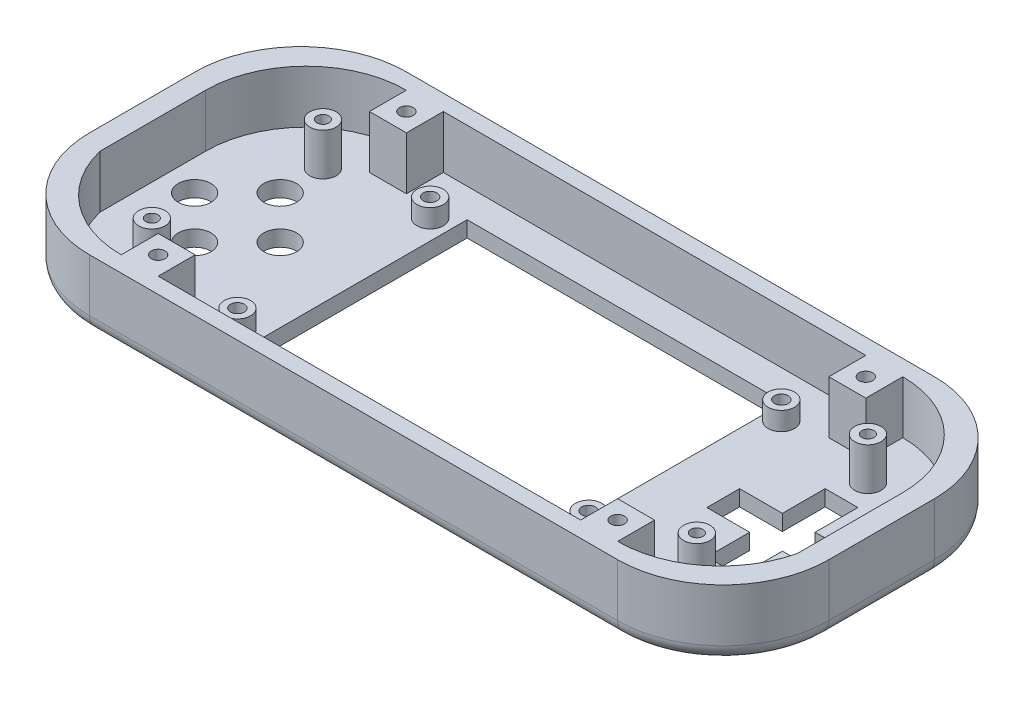
SolidWorks part; units mm, degrees
ref_plane "Front Plane" through (0, 0, 0) normal (0, 0, 1) x (1, 0, 0)
ref_plane "Top Plane" through (0, 0, 0) normal (0, 1, 0) x (1, 0, 0)
ref_plane "Right Plane" through (0, 0, 0) normal (1, 0, 0) x (0, 0, -1)
sketch "Sketch1" plane through (0, 0, 0) normal (0, 1, 0) x (1, 0, 0)
  line L0 (70, 10) -> (70, -10)
  line L1 (-50, 30) -> (50, 30)
  line L2 (-70, 10) -> (-70, -10)
  line L3 (-50, -30) -> (50, -30)
  line L5 (-50, 30) -> (50, -30) construction
  line L6 (-50, -30) -> (50, 30) construction
  arc A0 (-50, 30) -> (-70, 10) centre (-50, 10) ccw
  arc A1 (50, 30) -> (70, 10) centre (50, 10) cw
  arc A2 (-50, -30) -> (-70, -10) centre (-50, -10) cw
  arc A3 (50, -30) -> (70, -10) centre (50, -10) ccw
  point P0 (0, 0)
  dimension "D1" = 100
extrude "Boss-Extrude1" add sketch "Sketch1" along normal blind 3
sketch "Sketch2" plane through (0, 3, 0) normal (0, 1, 0) x (1, 0, 0)
  line L0 (-50, -30) -> (50, -30) construction
  line L1 (-47, 27) -> (47, 27)
  line L2 (-50, 30) -> (50, 30)
  line L3 (-47, -27) -> (47, -27)
  line L4 (70, 10) -> (70, -10)
  line L5 (-47, 27) -> (47, -27) construction
  line L6 (-47, -27) -> (47, 27) construction
  line L7 (-50, -30) -> (50, -30)
  line L8 (66, 8) -> (66, -12)
  line L9 (-50, 30) -> (50, -30) construction
  line L10 (-50, -30) -> (50, 30) construction
  line L11 (-70, 10) -> (-70, -10)
  line L13 (-66, 8) -> (-66, -12)
  arc A0 (-50, 30) -> (-70, 10) centre (-50, 10) ccw
  arc A1 (50, 30) -> (70, 10) centre (50, 10) cw
  arc A2 (-50, -30) -> (-70, -10) centre (-50, -10) cw
  arc A3 (50, -30) -> (70, -10) centre (50, -10) ccw
  arc A4 (47, 27) -> (66, 8) centre (47, 8) cw
  arc A5 (47, -27) -> (66, -12) centre (47, -7.4667) ccw
  arc A6 (-47, 27) -> (-66, 8) centre (-47, 8) ccw
  arc A7 (-47, -27) -> (-66, -12) centre (-47, -7.4667) cw
  point P0 (0, 0)
  point P8 (0, 0)
  dimension "D3" = 100
  dimension "D4" = 60
  dimension "D5" = 20
  dimension "D1" = 54
  dimension "D2" = 94
  dimension "D6" = 54
  dimension "D7" = 20
  dimension "D8" = 4
  dimension "D9" = 4
  dimension "D10" = 3
  dimension "D11" = 3
extrude "Boss-Extrude2" add sketch "Sketch2" along normal blind 10
sketch "Sketch3" plane through (0, 3, 0) normal (0, 1, 0) x (1, 0, 0)
  line L1 (-30, 21.5) -> (30, 21.5)
  line L2 (-30, 21.5) -> (-30, -21.5)
  line L3 (-30, -21.5) -> (30, -21.5)
  line L4 (30, 21.5) -> (30, -21.5)
  line L5 (-30, 21.5) -> (30, -21.5) construction
  line L6 (-30, -21.5) -> (30, 21.5) construction
  point P0 (0, 0)
  dimension "D1" = 43
  dimension "D2" = 60
extrude "Cut-Extrude1" cut sketch "Sketch3" against normal blind 5
sketch "Sketch4" plane through (0, 3, 0) normal (0, 1, 0) x (1, 0, 0)
  line L0 (30, 21.5) -> (-30, 21.5) construction
  line L1 (-30, 21.5) -> (-30, -21.5) construction
  line L2 (-30, -21.5) -> (30, -21.5) construction
  line L3 (30, -21.5) -> (30, 21.5) construction
  circle A0 centre (-33.75, 18.25) radius 2.5
  circle A1 centre (-33.75, -18.25) radius 2.5
  circle A2 centre (32.75, -18.25) radius 2.5
  circle A3 centre (32.75, 18.25) radius 2.5
  dimension "D1" = 5
  dimension "D4" = 5
  dimension "D5" = 3.25
  dimension "D7" = 5
  dimension "D10" = 5
  dimension "D2" = 3.25
  dimension "D3" = 3.75
  dimension "D6" = 3.75
  dimension "D8" = 3.25
  dimension "D9" = 2.75
  dimension "D11" = 2.75
  dimension "D12" = 3.25
extrude "Boss-Extrude3" add sketch "Sketch4" along normal blind 3.5
sketch "Sketch5" plane through (0, 6.5, 0) normal (0, 1, 0) x (1, 0, 0)
  circle A0 centre (-33.75, -18.25) radius 1.3
  dimension "D1" = 2.6
extrude "Cut-Extrude2" cut sketch "Sketch5" against normal blind 4.5
sketch "Sketch6" plane through (0, 6.5, 0) normal (0, 1, 0) x (1, 0, 0)
  circle A0 centre (-33.75, 18.25) radius 1.3
  dimension "D1" = 2.6
extrude "Cut-Extrude3" cut sketch "Sketch6" against normal blind 4.5
sketch "Sketch7" plane through (0, 6.5, 0) normal (0, 1, 0) x (1, 0, 0)
  circle A0 centre (32.75, 18.25) radius 1.3
  dimension "D1" = 2.6
extrude "Cut-Extrude4" cut sketch "Sketch7" against normal blind 4.5
sketch "Sketch8" plane through (0, 6.5, 0) normal (0, 1, 0) x (1, 0, 0)
  circle A0 centre (32.75, -18.25) radius 1.3
  dimension "D1" = 2.6
extrude "Cut-Extrude5" cut sketch "Sketch8" against normal blind 4.5
sketch "Sketch9" plane through (0, 3, 0) normal (0, 1, 0) x (1, 0, 0)
  line L0 (62.3, 3.2) -> (54.2, 3.2)
  line L1 (-30, 21.5) -> (-30, -21.5) construction
  line L3 (-47, -27) -> (47, -27) construction
  line L4 (30, 21.5) -> (30, -21.5) construction
  line L5 (46.1, 3.2) -> (39.9, 3.2)
  line L6 (62.3, -3) -> (54.2, -3)
  line L8 (54.2, -4.9) -> (54.2, -11.1)
  line L9 (54.2, -11.1) -> (48, -11.1)
  line L10 (48, -4.9) -> (48, -11.1)
  line L11 (54.2, -4.9) -> (48, -11.1) construction
  line L12 (54.2, -11.1) -> (48, -4.9) construction
  line L13 (46.1, -3) -> (39.9, -3)
  line L14 (39.9, 3.2) -> (39.9, -3)
  line L15 (46.1, 3.2) -> (39.9, -3) construction
  line L16 (46.1, -3) -> (39.9, 3.2) construction
  line L18 (62.3, 3.2) -> (62.3, -3)
  line L23 (54.2, 11.3) -> (48, 11.3)
  line L24 (54.2, 11.3) -> (54.2, 5.1)
  line L26 (48, 11.3) -> (48, 5.1)
  line L27 (54.2, 11.3) -> (48, 5.1) construction
  line L28 (54.2, 5.1) -> (48, 11.3) construction
  line L30 (54.2, -3) -> (54.2, -4.9)
  line L32 (54.2, 3.2) -> (54.2, 5.1)
  line L33 (48, 5.1) -> (48, 3.2)
  line L34 (48, 3.2) -> (46.1, 3.2)
  line L35 (46.1, -3) -> (48, -3)
  line L36 (48, -3) -> (48, -4.9)
  circle A4 centre (-44, 0.1) radius 3.1
  circle A5 centre (-52.1, 8.2) radius 3.1
  circle A6 centre (-60.2, 0.1) radius 3.1
  circle A7 centre (-52.1, -8) radius 3.1
  dimension "D3" = 9.9
  dimension "D4" = 6.2
  dimension "D5" = 6.2
  dimension "D6" = 8.1
  dimension "D7" = 6.2
  dimension "D8" = 6.2
  dimension "D9" = 6.2
  dimension "D10" = 6.2
  dimension "D11" = 8.1
  dimension "D12" = 6.2
  dimension "D13" = 6.2
  dimension "D14" = 6.2
  dimension "D15" = 6.2
  dimension "D16" = 8.1
  dimension "D17" = 14
  dimension "D18" = 8.1
  dimension "D19" = 8.1
  dimension "D20" = 8.1
  dimension "D21" = 8.1
  dimension "D22" = 8.1
  dimension "D23" = 1.9
  dimension "D24" = 19
  dimension "D25" = 8.1
  dimension "D26" = 11.4551
extrude "Cut-Extrude6" cut sketch "Sketch9" against normal blind 4.5
sketch "Sketch10" plane through (0, 3, 0) normal (0, 1, 0) x (1, 0, 0)
  line L1 (-47, -27) -> (47, -27) construction
  line L2 (30, -21.5) -> (30, 21.5) construction
  line L3 (-30, 21.5) -> (-30, -21.5) construction
  circle A0 centre (-52.1, -16.1) radius 2.5
  circle A1 centre (-52.1, 16.3) radius 2.5
  circle A2 centre (51.1, 16.3) radius 2.5
  circle A3 centre (51.1, -16.1) radius 2.5
  circle A4 centre (-52.1, -8) radius 3.1 construction
  circle A5 centre (-52.1, 8.2) radius 3.1 construction
  circle A6 centre (-52.1, 16.3) radius 1.15
  circle A7 centre (-52.1, -16.1) radius 1.15
  circle A8 centre (51.1, -16.1) radius 1.15
  circle A9 centre (51.1, 16.3) radius 1.15
  dimension "D1" = 5
  dimension "D2" = 5
  dimension "D3" = 5
  dimension "D4" = 5
  dimension "D5" = 8.1
  dimension "D6" = 8.1
  dimension "D7" = 0
  dimension "D8" = 0
  dimension "D9" = 22.1
  dimension "D10" = 10.9
  dimension "D11" = 2.3
  dimension "D12" = 2.3
  dimension "D13" = 2.3
  dimension "D14" = 2.3
  dimension "D15" = 21.1
  dimension "D16" = 21.1
extrude "Boss-Extrude4" add sketch "Sketch10" along normal blind 8
sketch "Sketch12" plane through (0, 3, 0) normal (0, 1, 0) x (1, 0, 0)
  line L0 (-47, -27) -> (47, -27) construction
  line L1 (-47, 27) -> (-40, 27)
  line L2 (-47, 27) -> (-47, 20)
  line L3 (-47, 20) -> (-40, 20)
  line L4 (-40, 27) -> (-40, 20)
  line L5 (-47, -27) -> (-40, -27)
  line L6 (-47, -27) -> (-47, -20)
  line L7 (-47, -20) -> (-40, -20)
  line L8 (-40, -27) -> (-40, -20)
  line L9 (47, -27) -> (40, -27)
  line L10 (47, -27) -> (47, -20)
  line L11 (47, -20) -> (40, -20)
  line L12 (40, -27) -> (40, -20)
  line L13 (47, 27) -> (40, 27)
  line L14 (47, 27) -> (47, 20)
  line L15 (47, 20) -> (40, 20)
  line L16 (40, 27) -> (40, 20)
  line L17 (-47, 27) -> (47, 27) construction
  dimension "D1" = 7
  dimension "D2" = 7
  dimension "D3" = 7
  dimension "D4" = 7
  dimension "D5" = 7
  dimension "D6" = 7
  dimension "D7" = 7
  dimension "D8" = 7
  dimension "D9" = 0
  dimension "D10" = 0
  dimension "D11" = 0
  dimension "D12" = 0
  dimension "D13" = 0
  dimension "D14" = 0
extrude "Boss-Extrude5" add sketch "Sketch12" along normal blind 10
fillet "Fillet1" radius 3 8 edges at (-64.1421, 0, 24.1421) (-64.1421, 0, -24.1421) (-70, 0, 0) (0, 0, 30) (64.1421, 0, 24.1421) (70, 0, 0) (64.1421, 0, -24.1421) (0, 0, -30)
sketch "Sketch13" plane through (0, 13, 0) normal (0, 1, 0) x (1, 0, 0)
  line L0 (47, 20) -> (47, 27) construction
  line L1 (40, 20) -> (47, 20) construction
  line L2 (47, -27) -> (47, -20) construction
  line L3 (47, -20) -> (40, -20) construction
  line L4 (-40, -27) -> (-40, -20) construction
  line L5 (-40, -20) -> (-47, -20) construction
  line L6 (-47, 20) -> (-40, 20) construction
  line L7 (-47, 27) -> (-47, 20) construction
  circle A0 centre (-43.5, 23.5) radius 1.3
  circle A1 centre (-43.5, -23.5) radius 1.3
  circle A2 centre (43.5, -23.5) radius 1.3
  circle A3 centre (43.5, 23.5) radius 1.3
  dimension "D1" = 2.6
  dimension "D2" = 2.6
  dimension "D3" = 2.6
  dimension "D4" = 2.6
  dimension "D7" = 3.5
  dimension "D8" = 3.5
  dimension "D9" = 3.5
  dimension "D11" = 3.5
  dimension "D12" = 3.5
  dimension "D5" = 3.5
  dimension "D6" = 3.5
  dimension "D10" = 3.5
extrude "Cut-Extrude7" cut sketch "Sketch13" against normal blind 9
